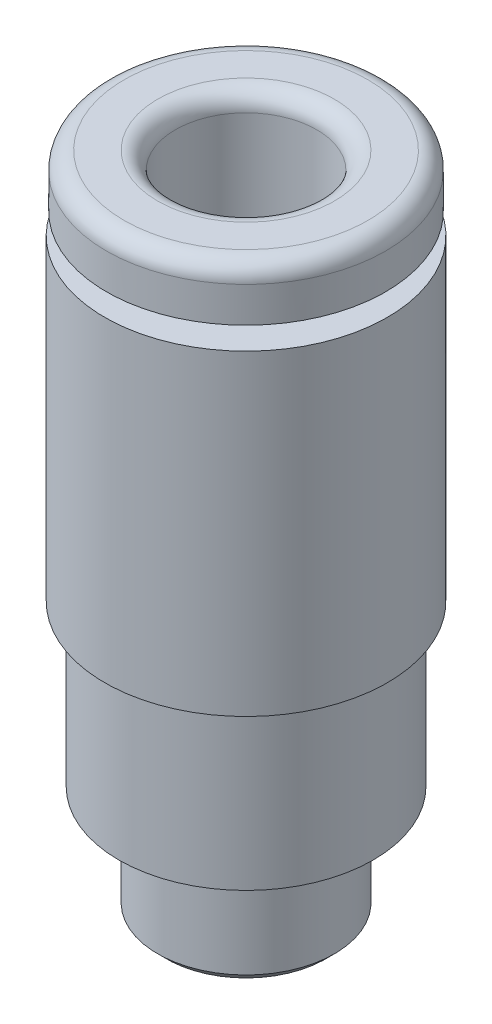
SolidWorks part; units mm, degrees
ref_plane "Front Plane" through (0, 0, 0) normal (0, 0, 1) x (1, 0, 0)
ref_plane "Top Plane" through (0, 0, 0) normal (0, 1, 0) x (1, 0, 0)
ref_plane "Right Plane" through (0, 0, 0) normal (1, 0, 0) x (0, 0, -1)
sketch "Sketch1" plane through (0, 0, 0) normal (0, 0, 1) x (1, 0, 0)
  line L0 (3.95, 0) -> (0, 0)
  line L1 (0, 0) -> (0, -15.6)
  line L2 (0, -15.6) -> (3.6, -15.6)
  line L3 (3.6, -15.6) -> (3.6, -11.2)
  line L4 (3.6, -11.2) -> (4, -11.0544)
  line L5 (4, -11.0544) -> (4, -2.1)
  line L6 (4, -2.1) -> (2.2, -2.1)
  line L7 (2.2, -2.1) -> (2.2, -1.5)
  line L8 (2.2, -1.5) -> (3.95, -1.5)
  line L9 (3.95, -1.5) -> (3.95, 0)
  line L10 (0, 0) -> (0, -15.6) construction
revolve "Revolve1" add sketch "Sketch1" angle 360 about L10
sketch "Sketch2" plane through (0, -15.6, 0) normal (0, -1, 0) x (1, 0, 0)
  circle A0 centre (0, 0) radius 2.5
extrude "Boss-Extrude1" add sketch "Sketch2" along normal blind 3.1
sketch "Sketch3" plane through (0, 0, 0) normal (0, 1, 0) x (-1, 0, 0)
  line L0 (0.9777, -1.6935) -> (1.9555, 0)
  line L1 (1.9555, 0) -> (0.9777, 1.6935)
  line L2 (0.9777, 1.6935) -> (-0.9777, 1.6935)
  line L3 (-0.9777, 1.6935) -> (-1.9555, 0)
  line L4 (-1.9555, 0) -> (-0.9777, -1.6935)
  line L5 (-0.9777, -1.6935) -> (0.9777, -1.6935)
extrude "Cut-Extrude1" cut sketch "Sketch3" against normal blind 14.7 draft 2
sketch "Sketch4" plane through (0, 0, 0) normal (1, 0, 0) x (0, 0, -1)
  line L0 (0, 0) -> (-2, 0)
  line L1 (-2, 0) -> (-2, -12.7)
  line L2 (-2, -12.7) -> (0, -12.7)
  line L3 (0, -12.7) -> (0, 0)
  line L4 (0, -12.7) -> (0, 0) construction
revolve "Cut-Revolve1" cut sketch "Sketch4" angle 360 about L4
hole_wizard "#2 Clearance Hole1" positions "Sketch6" profile "Sketch5" hole size "#2" standard "ANSI Inch"
sketch "Sketch6" plane through (0, -18.7, 0) normal (0, -1, 0) x (-1, 0, 0)
  point P0 (0, 0)
sketch "Sketch5" plane through (0, -18.7, 0) normal (1, 0, 0) x (0, 0, -1)
  line L0 (0, 0) -> (0, 18.7)
  line L1 (0, 18.7) -> (1.1802, 18.7)
  line L2 (1.1802, 18.7) -> (1.1802, 0)
  line L5 (1.1802, 0) -> (0, 0)
  line L11 (0, -6.35) -> (0, 107.95) construction
  dimension "Thru Hole Dia." = 2.3603
  dimension "Thru Hole Depth" = 18.7
chamfer "Chamfer1" distance 0.25 angle 45 1 edges at (0, -18.7, -2.5)
fillet "Fillet1" radius 0.5 2 edges at (0, 0, -3.95) (0, 0, 2)
